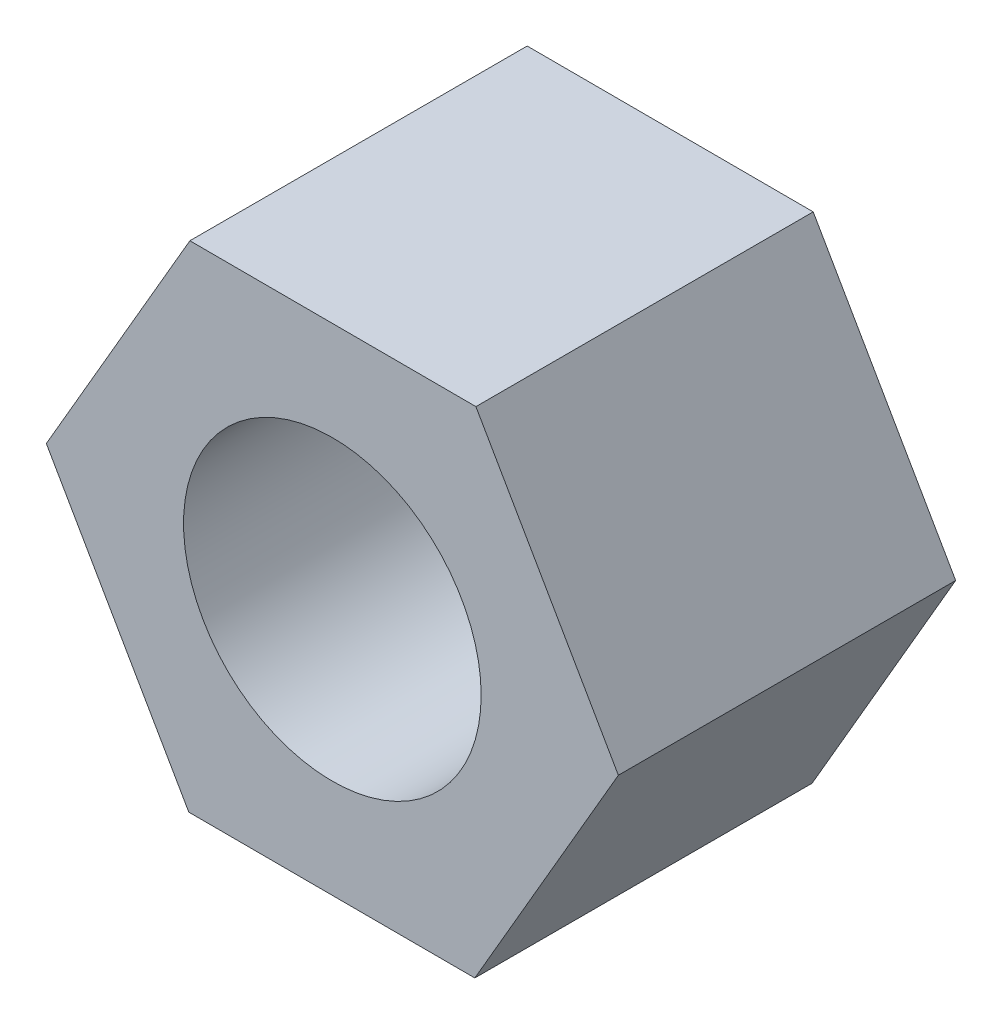
SolidWorks part; units mm, degrees
ref_plane "Płaszczyzna przednia" through (0, 0, 0) normal (0, 0, 1) x (1, 0, 0)
ref_plane "Płaszczyzna górna" through (0, 0, 0) normal (0, 1, 0) x (1, 0, 0)
ref_plane "Płaszczyzna prawa" through (0, 0, 0) normal (1, 0, 0) x (0, 0, -1)
sketch "Szkic1" plane through (0, 0, 0) normal (0, 0, 1) x (1, 0, 0)
  line L7 (-2.872, 5) -> (-5.7661, 0.0128)
  line L8 (-5.7661, 0.0128) -> (-2.8941, -4.9872)
  line L9 (-2.8941, -4.9872) -> (2.872, -5)
  line L10 (2.872, -5) -> (5.7661, -0.0128)
  line L11 (5.7661, -0.0128) -> (2.8941, 4.9872)
  line L12 (2.8941, 4.9872) -> (-2.872, 5)
  circle A1 centre (0, 0) radius 4.9936 construction
extrude "Dodanie-wyciągnięcie1" add sketch "Szkic1" along normal blind 6.8
sketch "Szkic2" plane through (0, 0, 0) normal (0, 0, 1) x (1, 0, 0)
  circle A0 centre (0, 0) radius 3
  dimension "D1" = 6
extrude "Wytnij-wyciągnięcie1" cut sketch "Szkic2" along normal blind 10.8
